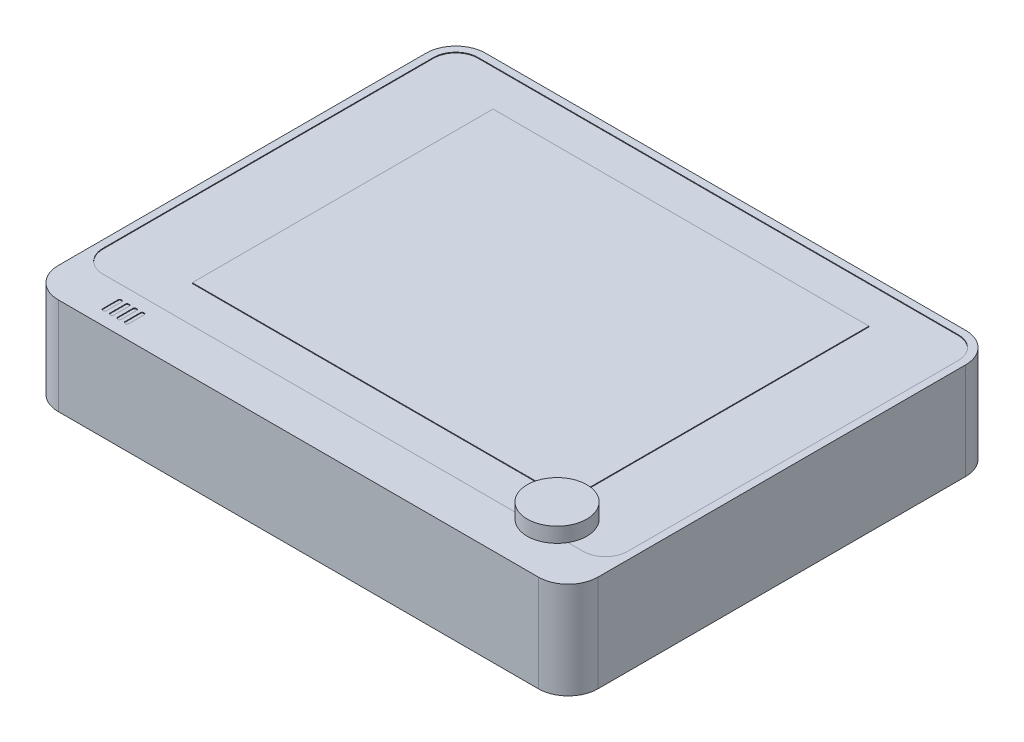
SolidWorks part; units mm, degrees
ref_plane "Front Plane" through (0, 0, 0) normal (0, 0, 1) x (1, 0, 0)
ref_plane "Top Plane" through (0, 0, 0) normal (0, 1, 0) x (1, 0, 0)
ref_plane "Right Plane" through (0, 0, 0) normal (1, 0, 0) x (0, 0, -1)
sketch "Sketch1" plane through (0, 0, 0) normal (0, 1, 0) x (1, 0, 0)
  line L1 (32.25, 28.7) -> (-32.25, 28.7)
  line L2 (36.25, 24.7) -> (36.25, -24.7)
  line L3 (32.25, -28.7) -> (-32.25, -28.7)
  line L4 (-36.25, 24.7) -> (-36.25, -24.7)
  line L5 (36.25, 28.7) -> (-36.25, -28.7) construction
  line L6 (36.25, -28.7) -> (-36.25, 28.7) construction
  arc A0 (36.25, -24.7) -> (32.25, -28.7) centre (32.25, -24.7) cw
  arc A1 (-32.25, -28.7) -> (-36.25, -24.7) centre (-32.25, -24.7) cw
  arc A2 (32.25, 28.7) -> (36.25, 24.7) centre (32.25, 24.7) cw
  arc A3 (-32.25, 28.7) -> (-36.25, 24.7) centre (-32.25, 24.7) ccw
  point P0 (0, 0)
  dimension "D3" = 4
  dimension "D1" = 57.4
  dimension "D2" = 72.5
extrude "Boss-Extrude1" add sketch "Sketch1" along normal blind 13
sketch "Sketch2" plane through (0, 13, 0) normal (0, 1, 0) x (1, 0, 0)
  line L4 (-27.25, -26.75) -> (-27.25, -24.65)
  line L6 (-32.25, -22.7) -> (32.25, -22.7)
  line L7 (-27.05, -24.45) -> (-26.95, -24.45)
  line L8 (35.25, -24.7) -> (35.25, 24.7)
  line L9 (32.25, 27.7) -> (-32.25, 27.7)
  line L10 (-35.25, 24.7) -> (-35.25, -24.7)
  line L11 (-32.25, -27.7) -> (32.25, -27.7)
  line L12 (35.25, -19.7) -> (35.25, 24.7)
  line L13 (32.25, 27.7) -> (-32.25, 27.7)
  line L14 (-35.25, 24.7) -> (-35.25, -19.7)
  line L17 (-26.75, -24.65) -> (-26.75, -26.75)
  line L18 (-26.95, -26.95) -> (-27.05, -26.95)
  line L19 (-28.25, -26.75) -> (-28.25, -24.65)
  line L20 (-28.05, -24.45) -> (-27.95, -24.45)
  line L21 (-27.75, -24.65) -> (-27.75, -26.75)
  line L22 (-27.95, -26.95) -> (-28.05, -26.95)
  line L23 (-26.25, -26.75) -> (-26.25, -24.65)
  line L24 (-26.05, -24.45) -> (-25.95, -24.45)
  line L25 (-25.75, -24.65) -> (-25.75, -26.75)
  line L26 (-25.95, -26.95) -> (-26.05, -26.95)
  line L27 (-25.25, -26.75) -> (-25.25, -24.65)
  line L28 (-25.05, -24.45) -> (-24.95, -24.45)
  line L29 (-24.75, -24.65) -> (-24.75, -26.75)
  line L30 (-24.95, -26.95) -> (-25.05, -26.95)
  arc A4 (35.25, -19.7) -> (32.25, -22.7) centre (32.25, -19.7) cw
  arc A5 (-32.25, -22.7) -> (-35.25, -19.7) centre (-32.25, -19.7) cw
  arc A6 (-27.75, -26.75) -> (-27.95, -26.95) centre (-27.95, -26.75) cw
  arc A7 (-28.25, -26.75) -> (-28.05, -26.95) centre (-28.05, -26.75) ccw
  arc A8 (32.25, -27.7) -> (35.25, -24.7) centre (32.25, -24.7) ccw
  arc A9 (35.25, 24.7) -> (32.25, 27.7) centre (32.25, 24.7) ccw
  arc A10 (-32.25, 27.7) -> (-35.25, 24.7) centre (-32.25, 24.7) ccw
  arc A11 (-35.25, -24.7) -> (-32.25, -27.7) centre (-32.25, -24.7) ccw
  arc A13 (35.25, 24.7) -> (32.25, 27.7) centre (32.25, 24.7) ccw
  arc A14 (-32.25, 27.7) -> (-35.25, 24.7) centre (-32.25, 24.7) ccw
  arc A16 (-27.95, -24.45) -> (-27.75, -24.65) centre (-27.95, -24.65) cw
  arc A17 (-28.25, -24.65) -> (-28.05, -24.45) centre (-28.05, -24.65) cw
  arc A18 (-26.75, -26.75) -> (-26.95, -26.95) centre (-26.95, -26.75) cw
  arc A19 (-27.25, -26.75) -> (-27.05, -26.95) centre (-27.05, -26.75) ccw
  arc A20 (-26.95, -24.45) -> (-26.75, -24.65) centre (-26.95, -24.65) cw
  arc A21 (-27.25, -24.65) -> (-27.05, -24.45) centre (-27.05, -24.65) cw
  arc A22 (-25.75, -26.75) -> (-25.95, -26.95) centre (-25.95, -26.75) cw
  arc A23 (-26.25, -26.75) -> (-26.05, -26.95) centre (-26.05, -26.75) ccw
  arc A24 (-25.95, -24.45) -> (-25.75, -24.65) centre (-25.95, -24.65) cw
  arc A25 (-26.25, -24.65) -> (-26.05, -24.45) centre (-26.05, -24.65) cw
  arc A26 (-24.75, -26.75) -> (-24.95, -26.95) centre (-24.95, -26.75) cw
  arc A27 (-25.25, -26.75) -> (-25.05, -26.95) centre (-25.05, -26.75) ccw
  arc A28 (-24.95, -24.45) -> (-24.75, -24.65) centre (-24.95, -24.65) cw
  arc A29 (-25.25, -24.65) -> (-25.05, -24.45) centre (-25.05, -24.65) cw
  point P19 (-21.4515, -25.7)
  dimension "D2" = 3
  dimension "D3" = 0.2
  dimension "D1" = 1
extrude "Cut-Extrude1" cut sketch "Sketch2" against normal blind 0.1
sketch "Sketch3" plane through (0, 12.9, 0) normal (0, 1, 0) x (1, 0, 0)
  line L9 (-25.25, 22.7) -> (25.25, 22.7)
  line L10 (-25.25, 22.7) -> (-25.25, -17.7)
  line L11 (-25.25, -17.7) -> (25.25, -17.7)
  line L12 (25.25, 22.7) -> (25.25, -17.7)
extrude "Boss-Extrude2" add sketch "Sketch3" along normal blind 0.1
sketch "Sketch4" plane through (0, 13, 0) normal (0, 1, 0) x (1, 0, 0)
  circle A0 centre (27.75, -21.7) radius 2
extrude "Boss-Extrude3" add sketch "Sketch4" along normal blind 1 and the other way blind 1
sketch "Sketch5" plane through (0, 14, 0) normal (0, 1, 0) x (1, 0, 0)
  circle A0 centre (27.75, -21.7) radius 4
extrude "Boss-Extrude4" add sketch "Sketch5" along normal blind 2
sketch "Sketch6" plane through (0, 0, 0) normal (0, -1, 0) x (1, 0, 0)
  circle A0 centre (30.75, 0) radius 1
  circle A1 centre (-30.75, 0) radius 1
extrude "Cut-Extrude3" cut sketch "Sketch6" against normal blind 2
